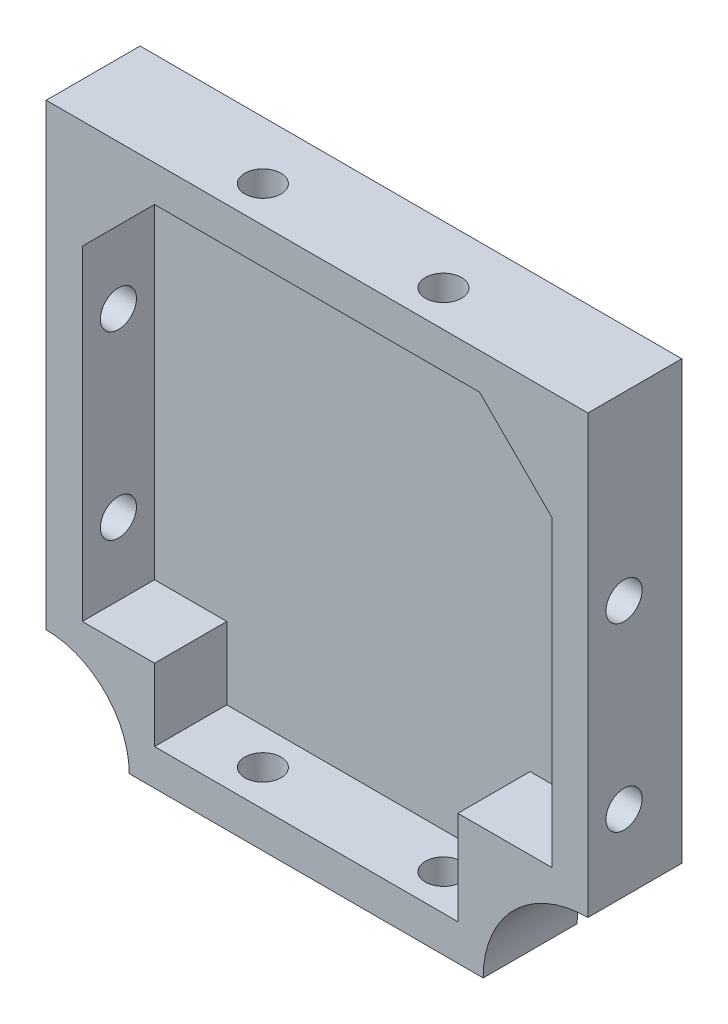
SolidWorks part; units mm, degrees
ref_plane "Plan de face" through (0, 0, 0) normal (0, 0, 1) x (1, 0, 0)
ref_plane "Plan de dessus" through (0, 0, 0) normal (0, 1, 0) x (1, 0, 0)
ref_plane "Plan de droite" through (0, 0, 0) normal (1, 0, 0) x (0, 0, -1)
sketch "Esquisse1" plane through (0, 0, 0) normal (0, 0, 1) x (1, 0, 0)
  line L0 (44.1184, 33.7284) -> (54.1184, 33.7284)
  line L1 (-20.8816, 33.7284) -> (44.1184, 33.7284)
  line L2 (-20.8816, 33.7284) -> (-20.8816, -41.2716)
  line L3 (-20.8816, -41.2716) -> (54.1184, -41.2716)
  line L4 (54.1184, 23.7284) -> (54.1184, -41.2716)
  line L5 (54.1184, 33.7284) -> (54.1184, 23.7284)
  point P6 (54.1184, 33.7284)
  dimension "D1" = 75
  dimension "D2" = 75
extrude "Boss.-Extru.1" add sketch "Esquisse1" along normal blind 13
shell "Coque1" thickness 5
sketch "Esquisse2" plane through (-20.8816, 0, 0) normal (-1, 0, 0) x (0, 0, 1)
  line L0 (13, 33.7284) -> (13, -41.2716) construction
  line L1 (13, 33.7284) -> (0, 33.7284) construction
  line L2 (13, -41.2716) -> (0, -41.2716) construction
  circle A0 centre (8, 8.7284) radius 2.5
  circle A1 centre (8, -16.2716) radius 2.5
  dimension "D1" = 5
  dimension "D2" = 5
  dimension "D3" = 5
  dimension "D4" = 5
  dimension "D5" = 25
  dimension "D6" = 25
extrude "Enlèv. mat.-Extru.1" cut sketch "Esquisse2" against normal up to surface (75 mm away) contours A1 | A0 up to face at (54.1184, -3.7716, 6.5)
sketch "Esquisse3" plane through (0, -41.2716, 0) normal (0, -1, 0) x (1, 0, 0)
  line L0 (-20.8816, 13) -> (54.1184, 13) construction
  line L2 (54.1184, 13) -> (54.1184, 0) construction
  line L3 (-20.8816, 13) -> (-20.8816, 0) construction
  circle A0 centre (4.1184, 8) radius 2.5
  circle A1 centre (29.1184, 8) radius 2.5
  dimension "D1" = 5
  dimension "D2" = 5
  dimension "D3" = 5
  dimension "D4" = 5
  dimension "D5" = 25
  dimension "D6" = 25
extrude "Enlèv. mat.-Extru.2" cut sketch "Esquisse3" against normal up to surface (75 mm away) up to face at (16.6184, 33.7284, 6.5)
sketch "Esquisse4" plane through (0, 0, 3) normal (0, 0, 1) x (1, 0, 0)
  line L0 (-5.8816, 28.7284) -> (-15.8816, 18.7284)
  line L1 (49.1184, 28.7284) -> (-15.8816, 28.7284) construction
  line L2 (-15.8816, 28.7284) -> (-15.8816, -36.2716) construction
  line L3 (-15.8816, 18.7284) -> (-15.8816, 28.7284)
  line L4 (-15.8816, 28.7284) -> (-5.8816, 28.7284)
  line L5 (49.1184, 28.7284) -> (49.1184, 18.7284)
  line L6 (49.1184, -36.2716) -> (49.1184, 28.7284) construction
  line L7 (49.1184, 18.7284) -> (39.1184, 28.7284)
  line L8 (39.1184, 28.7284) -> (49.1184, 28.7284)
  line L9 (49.1184, 28.7284) -> (-15.8816, 28.7284) construction
  line L11 (54.1184, -41.2716) -> (36.1184, -41.2716)
  line L13 (54.1184, -41.2716) -> (54.1184, -23.2716)
  line L14 (-20.8816, -26.2716) -> (-5.8816, -26.2716)
  line L15 (-20.8816, -41.2716) -> (54.1184, -41.2716) construction
  line L16 (-5.8816, -26.2716) -> (-5.8816, -41.2716)
  line L17 (-5.8816, -41.2716) -> (-20.8816, -41.2716)
  line L18 (-20.8816, -41.2716) -> (-20.8816, -26.2716)
  line L19 (-20.8816, 33.7284) -> (-20.8816, -41.2716) construction
  line L20 (54.1184, -23.2716) -> (36.1184, -23.2716)
  line L21 (36.1184, -41.2716) -> (36.1184, -23.2716)
  dimension "D1" = 10
  dimension "D2" = 10
  dimension "D3" = 10
  dimension "D4" = 10
  dimension "D5" = 18
  dimension "D6" = 18
  dimension "D7" = 15
  dimension "D8" = 15
  dimension "D9" = 0
  dimension "D10" = 0
extrude "Boss.-Extru.2" add sketch "Esquisse4" along normal up to surface (10 mm away) up to face at (16.6184, -3.7716, 13)
sketch "Esquisse5" plane through (0, 0, 13) normal (0, 0, 1) x (1, 0, 0)
  circle A0 centre (-20.8816, -41.2716) radius 11.5
  circle A1 centre (54.1184, -41.2716) radius 14.5
  dimension "D1" = 23
  dimension "D2" = 29
extrude "Enlèv. mat.-Extru.3" cut sketch "Esquisse5" against normal up to surface (13 mm away) up to face at (16.6184, -3.7716, 0)
